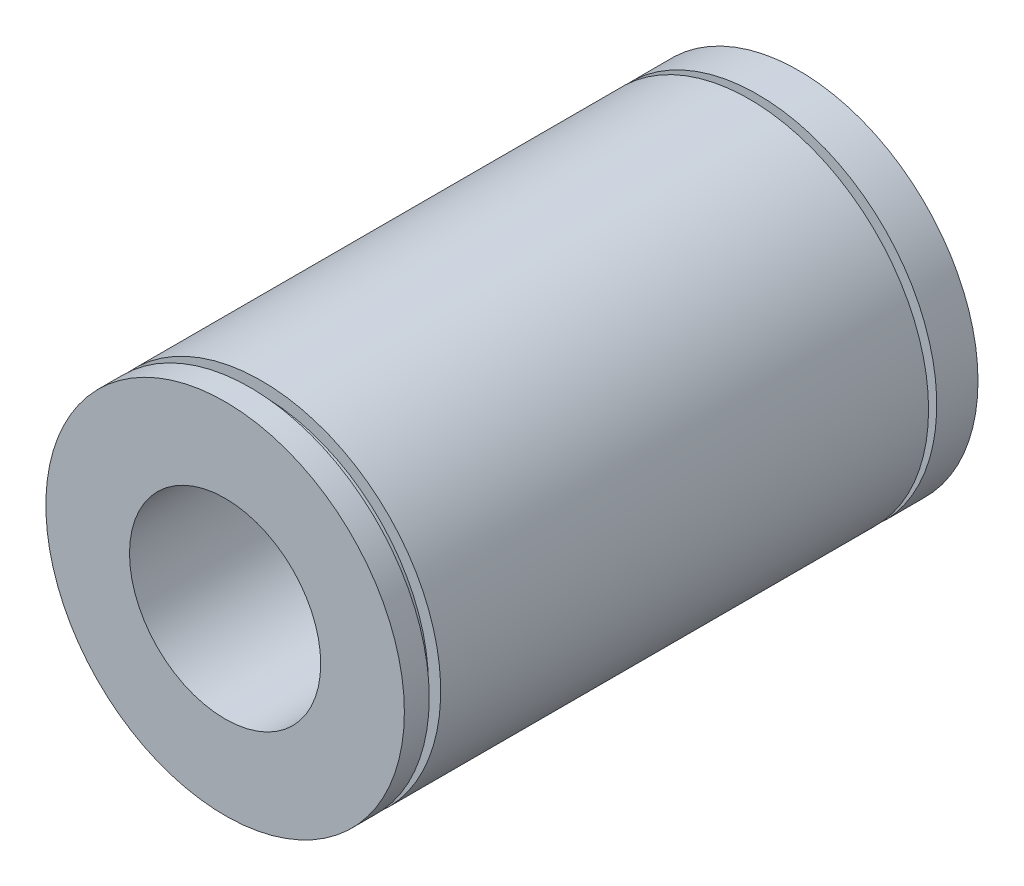
SolidWorks part; units mm, degrees
ref_plane "前视基准面" through (0, 0, 0) normal (0, 0, 1) x (1, 0, 0)
ref_plane "上视基准面" through (0, 0, 0) normal (0, 1, 0) x (1, 0, 0)
ref_plane "右视基准面" through (0, 0, 0) normal (1, 0, 0) x (0, 0, -1)
sketch "草图1" plane through (0, 0, 0) normal (0, 0, 1) x (1, 0, 0)
  circle A0 centre (0, 0) radius 4
  circle A1 centre (0, 0) radius 7.5
  dimension "D1" = 8
  dimension "D2" = 15
extrude "凸台-拉伸1" add sketch "草图1" along normal blind 24
sketch "草图2" plane through (0, 0, 0) normal (0, 1, 0) x (1, 0, 0)
  line L0 (7.5, -24) -> (7.5, 0) construction
  line L1 (6.9859, -1.7256) -> (8.0141, -1.7256)
  line L2 (6.9859, -1.7256) -> (6.9859, -2.068)
  line L3 (6.9859, -2.068) -> (8.0141, -2.068)
  line L4 (8.0141, -1.7256) -> (8.0141, -2.068)
  line L5 (6.9859, -1.7256) -> (8.0141, -2.068) construction
  line L6 (6.9859, -2.068) -> (8.0141, -1.7256) construction
  line L8 (6.9859, -22.4799) -> (8.0141, -22.4799)
  line L9 (6.9859, -22.4799) -> (6.9859, -22.9594)
  line L10 (6.9859, -22.9594) -> (8.0141, -22.9594)
  line L11 (8.0141, -22.4799) -> (8.0141, -22.9594)
  line L12 (6.9859, -22.4799) -> (8.0141, -22.9594) construction
  line L13 (6.9859, -22.9594) -> (8.0141, -22.4799) construction
  point P0 (7.5, -1.8968)
  point P7 (7.5, -22.7197)
ref_axis "基准轴1" through (0, 0, 0) along (0, 0, -1)
revolve "切除-旋转1" cut sketch "草图2" angle 360 about axis through (0, 0, 0) along (0, 0, -1)
